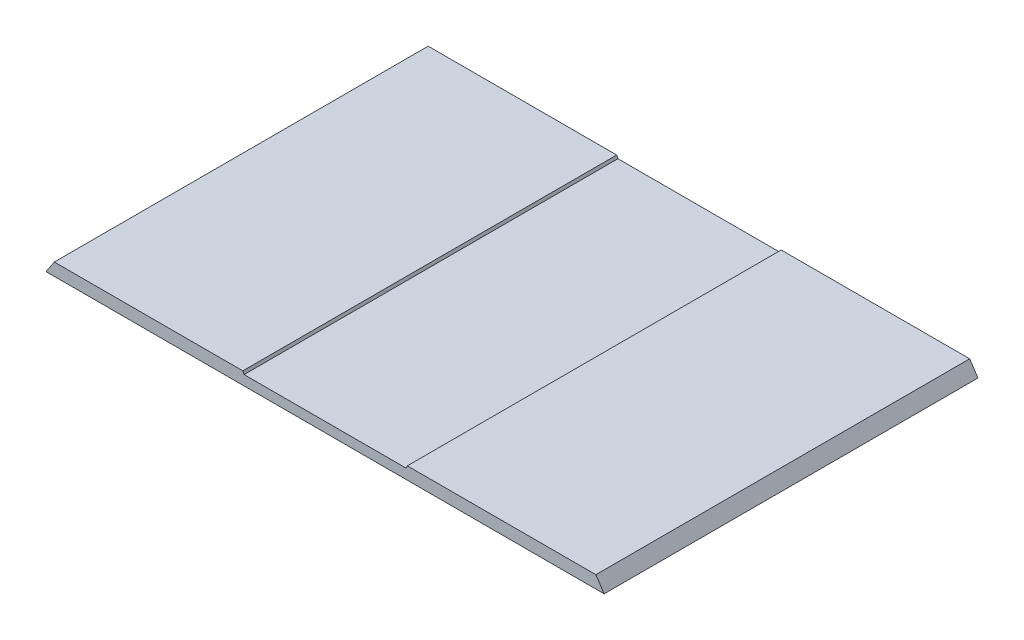
SolidWorks part; units mm, degrees
ref_plane "Ebene vorne" through (0, 0, 0) normal (0, 0, 1) x (1, 0, 0)
ref_plane "Ebene oben" through (0, 0, 0) normal (0, 1, 0) x (1, 0, 0)
ref_plane "Ebene rechts" through (0, 0, 0) normal (1, 0, 0) x (0, 0, -1)
sketch "Skizze1" plane through (0, 0, 0) normal (0, 0, 1) x (1, 0, 0)
  line L0 (-325.9142, -179.3676) -> (-335.9142, -194.3676)
  line L1 (-99, -179.3676) -> (-97.5, -182.5)
  line L2 (335.9142, -194.3676) -> (-335.9142, -194.3676)
  line L3 (99, -179.3676) -> (97.5, -182.5)
  line L4 (325.9142, -179.3676) -> (335.9142, -194.3676)
  line L10 (97.5, -182.5) -> (-97.5, -182.5)
  line L19 (-99, -179.3676) -> (-325.9142, -179.3676)
  line L40 (99, -179.3676) -> (325.9142, -179.3676)
extrude "Aufsatz-Linear austragen1" add sketch "Skizze1" along normal blind 450
